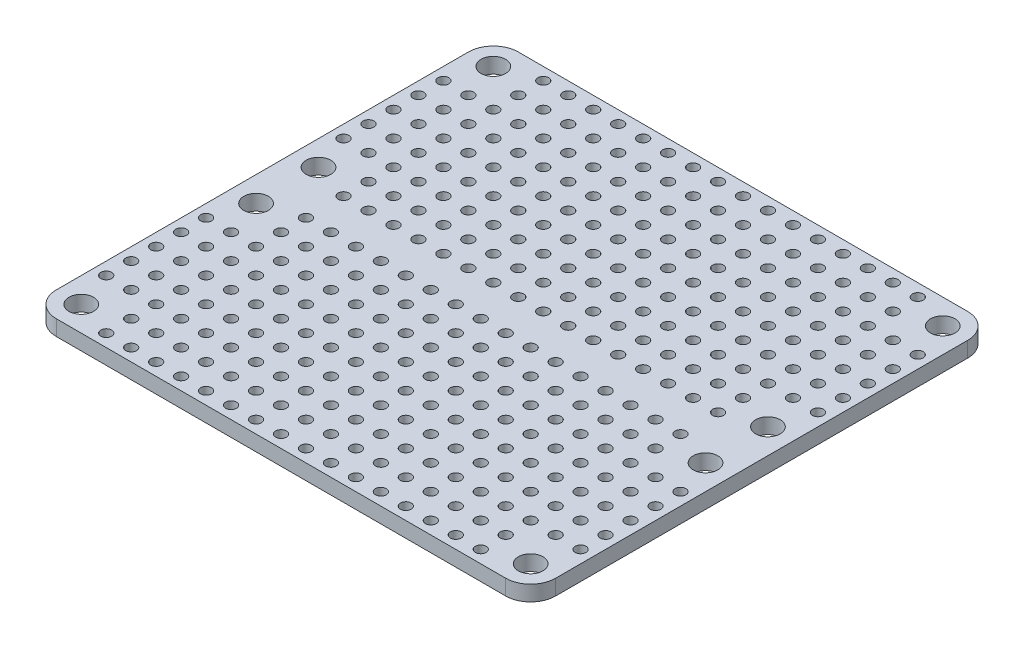
SolidWorks part; units mm, degrees
ref_plane "Front Plane" through (0, 0, 0) normal (0, 0, 1) x (1, 0, 0)
ref_plane "Top Plane" through (0, 0, 0) normal (0, 1, 0) x (1, 0, 0)
ref_plane "Right Plane" through (0, 0, 0) normal (1, 0, 0) x (0, 0, -1)
sketch "Sketch1" plane through (0, 0, 0) normal (0, 1, 0) x (1, 0, 0)
  line L0 (0, 23.5) -> (50.8, 23.5) construction
  line L1 (0, 0) -> (50.8, 0)
  line L2 (0, 0) -> (0, 47)
  line L3 (0, 47) -> (50.8, 47)
  line L4 (50.8, 0) -> (50.8, 47)
  line L5 (25.4, 47) -> (25.4, 0) construction
  line L6 (2.54, 47) -> (2.54, 23.5) construction
  circle A0 centre (2.54, 44.46) radius 1.25
  circle A1 centre (2.54, 26.675) radius 1.25
  circle A2 centre (48.26, 26.675) radius 1.25
  circle A3 centre (48.26, 44.46) radius 1.25
  circle A4 centre (48.26, 20.325) radius 1.25
  circle A5 centre (48.26, 2.54) radius 1.25
  circle A6 centre (2.54, 2.54) radius 1.25
  circle A7 centre (2.54, 20.325) radius 1.25
  dimension "D3" = 2.5
  dimension "D1" = 47
  dimension "D2" = 50.8
  dimension "D4" = 2.54
  dimension "D5" = 2.54
  dimension "D6" = 3.175
extrude "Boss-Extrude1" add sketch "Sketch1" along normal blind 1.57
ref_plane "Plane1" through (25.4, 0, 0) normal (-1, 0, 0) x (0, 0, 1)
ref_plane "Plane2" through (0, 0, -23.5) normal (0, 0, 1) x (1, 0, 0)
sketch "Sketch4" plane through (0, 0, 0) normal (0, 1, 0) x (1, 0, 0)
  line L0 (0, 45.73) -> (25.4, 45.73) construction
  line L1 (0, 0) -> (0, 47) construction
  line L2 (25.4, 47) -> (25.4, 0) construction
  line L3 (0, 47) -> (50.8, 47) construction
  line L4 (6.35, 45.73) -> (8.89, 45.73) construction
  line L5 (6.35, 43.19) -> (8.89, 43.19) construction
  line L6 (6.35, 40.65) -> (8.89, 40.65) construction
  line L7 (6.35, 38.11) -> (8.89, 38.11) construction
  line L8 (6.35, 35.57) -> (8.89, 35.57) construction
  line L9 (6.35, 33.03) -> (8.89, 33.03) construction
  line L10 (6.35, 30.49) -> (8.89, 30.49) construction
  line L11 (6.35, 27.95) -> (8.89, 27.95) construction
  line L12 (6.35, 25.41) -> (8.89, 25.41) construction
  line L13 (6.35, 45.73) -> (6.35, 43.19) construction
  line L14 (6.35, 40.65) -> (3.81, 40.65) construction
  circle A0 centre (6.35, 45.73) radius 0.55
  circle A1 centre (8.89, 45.73) radius 0.55
  circle A2 centre (11.43, 45.73) radius 0.55
  circle A3 centre (13.97, 45.73) radius 0.55
  circle A4 centre (16.51, 45.73) radius 0.55
  circle A5 centre (19.05, 45.73) radius 0.55
  circle A6 centre (21.59, 45.73) radius 0.55
  circle A7 centre (24.13, 45.73) radius 0.55
  circle A8 centre (6.35, 43.19) radius 0.55
  circle A9 centre (8.89, 43.19) radius 0.55
  circle A10 centre (11.43, 43.19) radius 0.55
  circle A11 centre (13.97, 43.19) radius 0.55
  circle A12 centre (16.51, 43.19) radius 0.55
  circle A13 centre (19.05, 43.19) radius 0.55
  circle A14 centre (21.59, 43.19) radius 0.55
  circle A15 centre (24.13, 43.19) radius 0.55
  circle A16 centre (6.35, 40.65) radius 0.55
  circle A17 centre (8.89, 40.65) radius 0.55
  circle A18 centre (11.43, 40.65) radius 0.55
  circle A19 centre (13.97, 40.65) radius 0.55
  circle A20 centre (16.51, 40.65) radius 0.55
  circle A21 centre (19.05, 40.65) radius 0.55
  circle A22 centre (21.59, 40.65) radius 0.55
  circle A23 centre (24.13, 40.65) radius 0.55
  circle A24 centre (6.35, 38.11) radius 0.55
  circle A25 centre (8.89, 38.11) radius 0.55
  circle A26 centre (11.43, 38.11) radius 0.55
  circle A27 centre (13.97, 38.11) radius 0.55
  circle A28 centre (16.51, 38.11) radius 0.55
  circle A29 centre (19.05, 38.11) radius 0.55
  circle A30 centre (21.59, 38.11) radius 0.55
  circle A31 centre (24.13, 38.11) radius 0.55
  circle A32 centre (6.35, 35.57) radius 0.55
  circle A33 centre (8.89, 35.57) radius 0.55
  circle A34 centre (11.43, 35.57) radius 0.55
  circle A35 centre (13.97, 35.57) radius 0.55
  circle A36 centre (16.51, 35.57) radius 0.55
  circle A37 centre (19.05, 35.57) radius 0.55
  circle A38 centre (21.59, 35.57) radius 0.55
  circle A39 centre (24.13, 35.57) radius 0.55
  circle A40 centre (6.35, 33.03) radius 0.55
  circle A41 centre (8.89, 33.03) radius 0.55
  circle A42 centre (11.43, 33.03) radius 0.55
  circle A43 centre (13.97, 33.03) radius 0.55
  circle A44 centre (16.51, 33.03) radius 0.55
  circle A45 centre (19.05, 33.03) radius 0.55
  circle A46 centre (21.59, 33.03) radius 0.55
  circle A47 centre (24.13, 33.03) radius 0.55
  circle A48 centre (6.35, 30.49) radius 0.55
  circle A49 centre (8.89, 30.49) radius 0.55
  circle A50 centre (11.43, 30.49) radius 0.55
  circle A51 centre (13.97, 30.49) radius 0.55
  circle A52 centre (16.51, 30.49) radius 0.55
  circle A53 centre (19.05, 30.49) radius 0.55
  circle A54 centre (21.59, 30.49) radius 0.55
  circle A55 centre (24.13, 30.49) radius 0.55
  circle A56 centre (6.35, 27.95) radius 0.55
  circle A57 centre (8.89, 27.95) radius 0.55
  circle A58 centre (11.43, 27.95) radius 0.55
  circle A59 centre (13.97, 27.95) radius 0.55
  circle A60 centre (16.51, 27.95) radius 0.55
  circle A61 centre (19.05, 27.95) radius 0.55
  circle A62 centre (21.59, 27.95) radius 0.55
  circle A63 centre (24.13, 27.95) radius 0.55
  circle A64 centre (6.35, 25.41) radius 0.55
  circle A65 centre (8.89, 25.41) radius 0.55
  circle A66 centre (11.43, 25.41) radius 0.55
  circle A67 centre (13.97, 25.41) radius 0.55
  circle A68 centre (16.51, 25.41) radius 0.55
  circle A69 centre (19.05, 25.41) radius 0.55
  circle A70 centre (21.59, 25.41) radius 0.55
  circle A71 centre (24.13, 25.41) radius 0.55
  circle A72 centre (3.81, 40.65) radius 0.55
  circle A73 centre (3.81, 38.11) radius 0.55
  circle A74 centre (3.81, 35.57) radius 0.55
  circle A75 centre (3.81, 33.03) radius 0.55
  circle A76 centre (3.81, 30.49) radius 0.55
  circle A77 centre (1.27, 40.65) radius 0.55
  circle A78 centre (1.27, 38.11) radius 0.55
  circle A79 centre (1.27, 35.57) radius 0.55
  circle A80 centre (1.27, 33.03) radius 0.55
  circle A81 centre (1.27, 30.49) radius 0.55
  dimension "D2" = 1.1
  dimension "D1" = 1.27
  dimension "D3" = 6.35
  dimension "D5" = 2.54
  dimension "D7" = 2.54
  dimension "D9" = 2.54
  dimension "D4" = 8
  dimension "D6" = 9
  dimension "D8" = 3
extrude "Cut-Extrude2" cut sketch "Sketch4" along normal through all
mirror "Mirror1" about plane through (25.4, 0, 0) normal (-1, 0, 0) of "Cut-Extrude2"
mirror "Mirror2" about plane through (0, 0, -23.5) normal (0, 0, 1) of "Cut-Extrude2", "Mirror1"
fillet "Fillet1" radius 2.54 4 edges at (50.8, 0.785, 0) (0, 0.785, 0) (0, 0.785, -47) (50.8, 0.785, -47)
